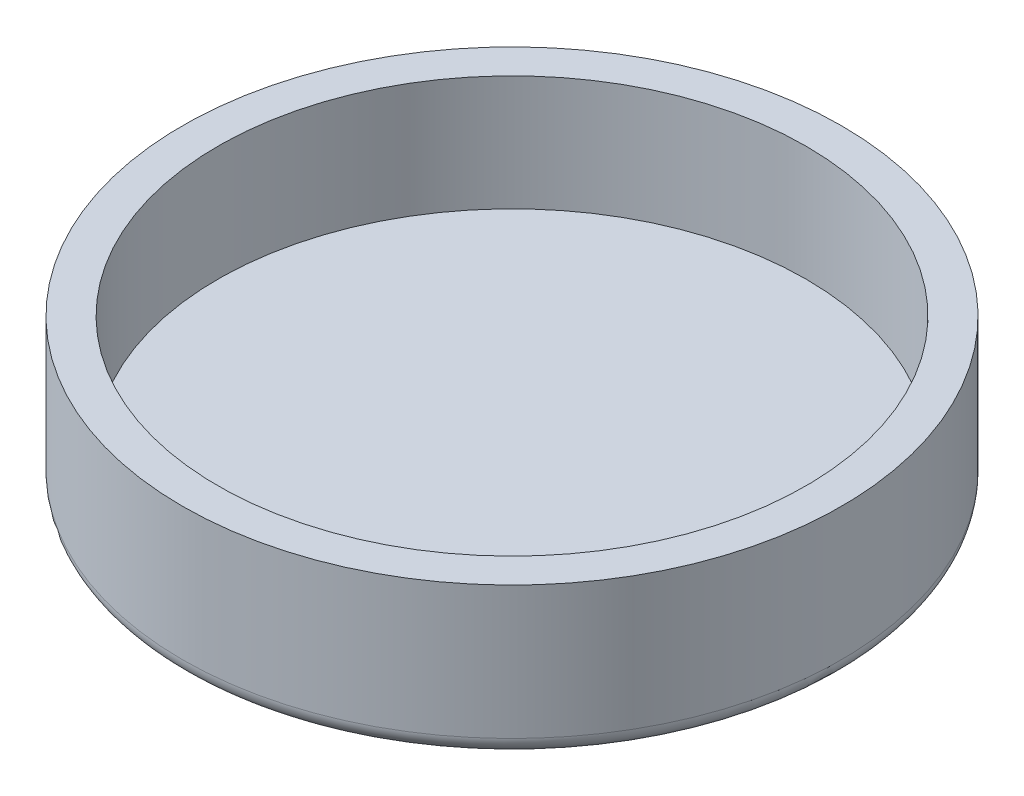
SolidWorks part; units mm, degrees
material "Brass"
ref_plane "Front Plane" through (0, 0, 0) normal (0, 0, 1) x (1, 0, 0)
ref_plane "Top Plane" through (0, 0, 0) normal (0, 1, 0) x (1, 0, 0)
ref_plane "Right Plane" through (0, 0, 0) normal (1, 0, 0) x (0, 0, -1)
sketch "Sketch1" plane through (0, 0, 0) normal (0, 0, 1) x (1, 0, 0)
  line L6 (0, 0) -> (-8.8, 0)
  line L7 (-9.3, 0.5) -> (-9.3, 4.25)
  line L8 (-9.3, 4.25) -> (-8.3, 4.25)
  line L9 (-8.3, 4.25) -> (-8.3, 1)
  line L10 (-8.3, 1) -> (-1, 1)
  line L11 (0, 0.9) -> (0, 0)
  line L12 (0, 0) -> (0, 0.9) construction
  line L15 (0, 1) -> (0, 5.6222) construction
  line L16 (-1, 1) -> (0, 1)
  line L17 (0, 1) -> (0, 0.9)
  arc A0 (-8.8, 0) -> (-9.3, 0.5) centre (-8.8, 0.5) cw
  dimension "D3" = 0.5
  dimension "D1" = 1
  dimension "D2" = 1
  dimension "D4" = 4.25
  dimension "D5" = 9.3
revolve "Revolve1" add sketch "Sketch1" angle 360 about L15
